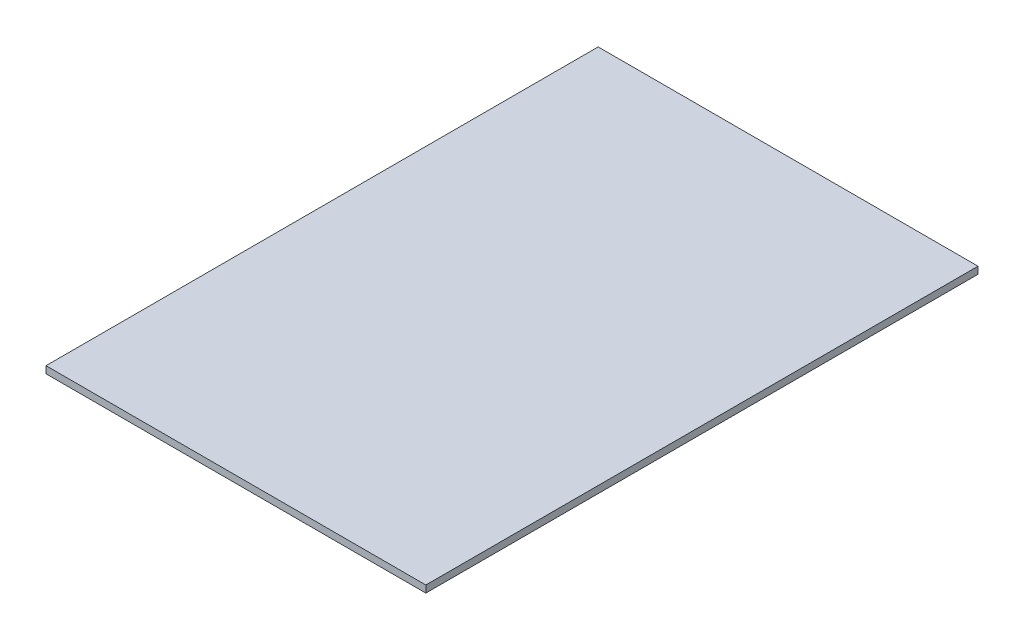
SolidWorks part; units mm, degrees
ref_plane "Front Plane" through (0, 0, 0) normal (0, 0, 1) x (1, 0, 0)
ref_plane "Top Plane" through (0, 0, 0) normal (0, 1, 0) x (1, 0, 0)
ref_plane "Right Plane" through (0, 0, 0) normal (1, 0, 0) x (0, 0, -1)
sketch "Sketch1" plane through (0, 0, 0) normal (0, 1, 0) x (1, 0, 0)
  line L1 (-270, -392.5) -> (270, -392.5)
  line L2 (-270, -392.5) -> (-270, 392.5)
  line L3 (-270, 392.5) -> (270, 392.5)
  line L4 (270, -392.5) -> (270, 392.5)
  line L5 (-270, -392.5) -> (270, 392.5) construction
  line L6 (-270, 392.5) -> (270, -392.5) construction
  point P0 (0, 0)
  dimension "D1" = 540
  dimension "D2" = 785
extrude "Boss-Extrude1" add sketch "Sketch1" along normal blind 10 contours L2 L3 L4 L1
